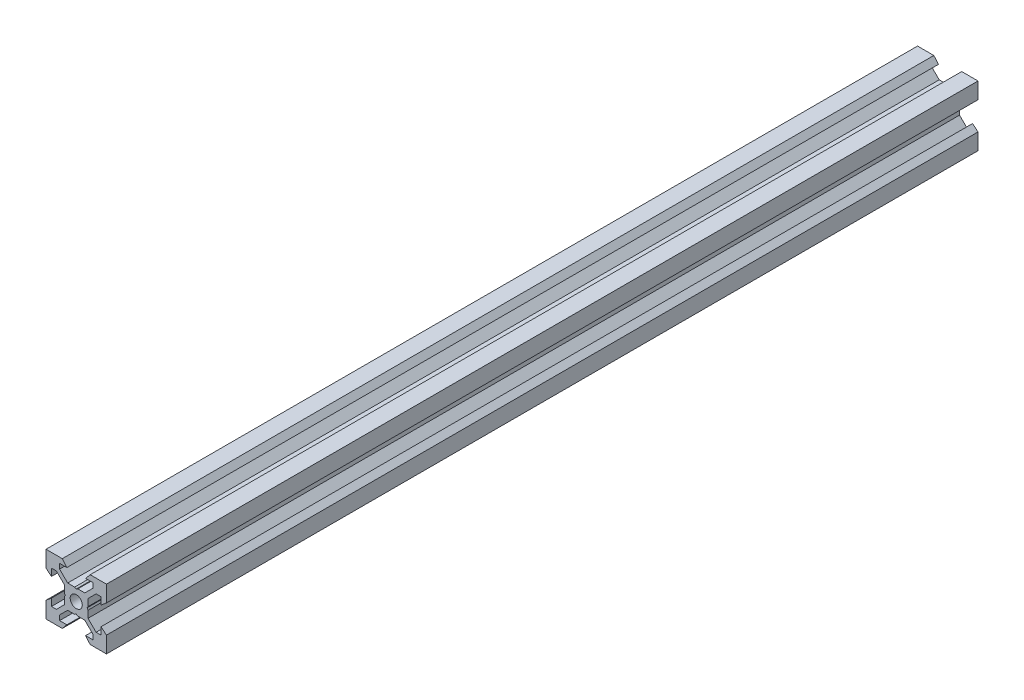
SolidWorks part; units mm, degrees
ref_plane "Front Plane" through (0, 0, 0) normal (0, 0, 1) x (1, 0, 0)
ref_plane "Top Plane" through (0, 0, 0) normal (0, 1, 0) x (1, 0, 0)
ref_plane "Right Plane" through (0, 0, 0) normal (1, 0, 0) x (0, 0, -1)
sketch "Sketch1" plane through (0, 0, 0) normal (0, 0, 1) x (1, 0, 0)
  line L0 (10, 10) -> (4.6104, 10) construction
  line L1 (10, 10) -> (10, 4.6104) construction
  line L2 (10, -10) -> (10, -4.6104) construction
  line L3 (10, -10) -> (4.6104, -10) construction
  line L4 (10, 10) -> (10, 4.6104)
  line L5 (6.5607, 5.5) -> (8.2, 5.5)
  line L6 (5.5, 8.2) -> (5.5, 6.5607)
  line L7 (10, 10) -> (4.6104, 10)
  line L8 (10, 10) -> (10, 4.6104)
  line L9 (6.5607, 5.5) -> (3.9, 2.8393)
  line L10 (5.5, 6.5607) -> (2.8393, 3.9)
  line L11 (10, 4.6104) -> (8.2, 3.1)
  line L12 (4.6104, 10) -> (3.1, 8.2)
  line L13 (8.2, 3.1) -> (8.2, 5.5)
  line L14 (3.1, 8.2) -> (5.5, 8.2)
  line L15 (-6.5607, 5.5) -> (-8.2, 5.5)
  line L16 (6.5607, -5.5) -> (8.2, -5.5)
  line L17 (3.1, -8.2) -> (5.5, -8.2)
  line L18 (8.2, -3.1) -> (8.2, -5.5)
  line L19 (4.6104, -10) -> (3.1, -8.2)
  line L20 (10, -4.6104) -> (8.2, -3.1)
  line L21 (0.5196, -3.9) -> (0, -3.6)
  line L22 (0.5196, 3.9) -> (0, 3.6)
  line L23 (3.6, 0) -> (3.9, -0.5196)
  line L24 (3.9, 0.5196) -> (3.6, 0)
  line L25 (3.9, 0.5196) -> (3.9, 2.8393)
  line L26 (2.8393, 3.9) -> (0.5196, 3.9)
  line L27 (3.9, -2.8393) -> (3.9, -0.5196)
  line L28 (2.8393, -3.9) -> (0.5196, -3.9)
  line L29 (5.5, -6.5607) -> (2.8393, -3.9)
  line L30 (6.5607, -5.5) -> (3.9, -2.8393)
  line L31 (10, -10) -> (10, -4.6104)
  line L32 (10, -10) -> (4.6104, -10)
  line L33 (5.5, -8.2) -> (5.5, -6.5607)
  line L34 (-6.5607, -5.5) -> (-8.2, -5.5)
  line L35 (10, -10) -> (10, -4.6104)
  line L36 (0, 0) -> (0, 8.2) construction
  line L37 (-10, -10) -> (-4.6104, -10) construction
  line L38 (-10, -10) -> (-10, -4.6104) construction
  line L39 (-10, 10) -> (-10, 4.6104) construction
  line L40 (-10, 10) -> (-4.6104, 10) construction
  line L41 (-10, -10) -> (-10, -4.6104)
  line L43 (-5.5, -8.2) -> (-5.5, -6.5607)
  line L44 (-10, -10) -> (-4.6104, -10)
  line L45 (-10, -10) -> (-10, -4.6104)
  line L46 (-6.5607, -5.5) -> (-3.9, -2.8393)
  line L47 (-5.5, -6.5607) -> (-2.8393, -3.9)
  line L48 (-2.8393, -3.9) -> (-0.5196, -3.9)
  line L49 (-3.9, -2.8393) -> (-3.9, -0.5196)
  line L50 (-2.8393, 3.9) -> (-0.5196, 3.9)
  line L51 (-3.9, 0.5196) -> (-3.9, 2.8393)
  line L52 (-3.9, 0.5196) -> (-3.6, 0)
  line L53 (-3.6, 0) -> (-3.9, -0.5196)
  line L54 (-0.5196, 3.9) -> (0, 3.6)
  line L55 (-0.5196, -3.9) -> (0, -3.6)
  line L56 (-10, -4.6104) -> (-8.2, -3.1)
  line L57 (-4.6104, -10) -> (-3.1, -8.2)
  line L58 (-8.2, -3.1) -> (-8.2, -5.5)
  line L59 (-3.1, -8.2) -> (-5.5, -8.2)
  line L60 (-10, -10) -> (10, -10) construction
  line L61 (-10, -10) -> (-10, 10) construction
  line L62 (-3.1, 8.2) -> (-5.5, 8.2)
  line L63 (-8.2, 3.1) -> (-8.2, 5.5)
  line L64 (-4.6104, 10) -> (-3.1, 8.2)
  line L65 (-10, 4.6104) -> (-8.2, 3.1)
  line L66 (-5.5, 6.5607) -> (-2.8393, 3.9)
  line L67 (-6.5607, 5.5) -> (-3.9, 2.8393)
  line L68 (-10, 10) -> (-10, 4.6104)
  line L69 (-10, 10) -> (-4.6104, 10)
  line L70 (-5.5, 8.2) -> (-5.5, 6.5607)
  line L71 (-10, 10) -> (10, 10) construction
  line L72 (-10, 10) -> (-10, 4.6104)
  line L73 (10, -10) -> (10, 10) construction
  line L74 (-10, -10) -> (10, 10) construction
  line L75 (-10, 10) -> (10, -10) construction
  circle A0 centre (0, 0) radius 2
  dimension "D7" = 4
  dimension "D1" = 20
  dimension "D2" = 5.3896
  dimension "D3" = 4.5
  dimension "D4" = 50
  dimension "D5" = 1.8
  dimension "D6" = 1.5104
  dimension "D8" = 5.5
  dimension "D9" = 120
  dimension "D10" = 0.3
  dimension "D11" = 2.3197
  dimension "D12" = 7.8
  dimension "D13" = 7.8
  dimension "D14" = 1.5
  dimension "D15" = 2.6607
extrude "Boss-Extrude1" add sketch "Sketch1" along normal mid plane 288.33 contours L70 L62 L64 L69 L68 L65 L63 L15 L67 L51 L52 L53 L49 L46 L34 L58 L56 L41 L44 L57 L59 L43 L47 L48 L55 L21 L28 L29 L33 L17 L19 L32 L31 L20 L18 L16 L30 L27 L23 L24 L25 L9 L5 L13 L11 L4 L7 L12 L14 L6 L10
